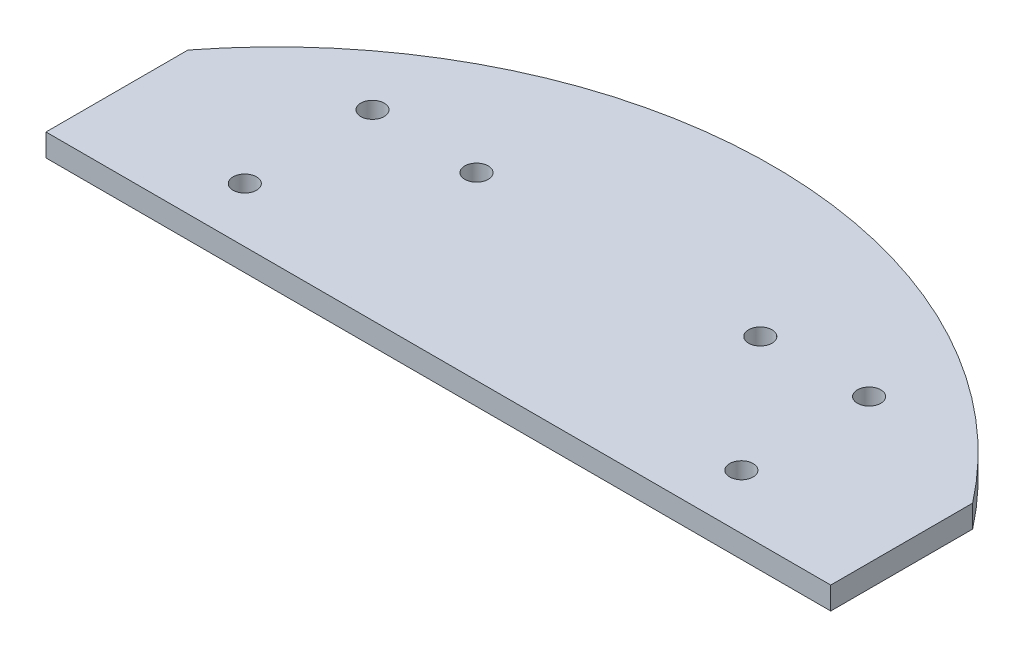
SolidWorks part; units mm, degrees
ref_plane "Front Plane" through (0, 0, 0) normal (0, 0, 1) x (1, 0, 0)
ref_plane "Top Plane" through (0, 0, 0) normal (0, 1, 0) x (1, 0, 0)
ref_plane "Right Plane" through (0, 0, 0) normal (1, 0, 0) x (0, 0, -1)
sketch "Sketch1" plane through (0, 0, 0) normal (0, 1, 0) x (1, 0, 0)
  line L0 (0, 70) -> (0, 22.9088) construction
  line L1 (35, 22.9088) -> (35, 60.6218) construction
  line L3 (0, 0) -> (49.4975, 49.4975) construction
  line L4 (0, 0) -> (26.7878, 64.6716) construction
  line L15 (0, 0) -> (-26.7878, 64.6716) construction
  line L16 (0, 0) -> (-49.4975, 49.4975) construction
  line L18 (-55.3067, 42.9088) -> (-55.3067, 22.9088)
  line L19 (55.3067, 42.9088) -> (55.3067, 22.9088)
  line L20 (-55.3067, 22.9088) -> (55.3067, 22.9088)
  arc A14 (55.3067, 42.9088) -> (-55.3067, 42.9088) centre (0, 0) ccw
  circle A17 centre (35, 48.6218) radius 1.65
  circle A18 centre (35, 30.6218) radius 1.65
  circle A19 centre (-35, 30.6218) radius 1.65
  circle A20 centre (-35, 48.6218) radius 1.65
  circle A21 centre (20, 48.2843) radius 1.65
  circle A22 centre (-20, 48.2843) radius 1.65
  point P21 (0, 0)
  point P22 (0, 0)
  point P23 (0, 0)
  dimension "D1" = 3.3
  dimension "D5" = 12
  dimension "D9" = 20
  dimension "D6" = 3.3
  dimension "D2" = 35
  dimension "D3" = 18
  dimension "D4" = 22.5
  dimension "D7" = 20
  dimension "D8" = 45
  dimension "D10" = 22.5
  dimension "D11" = 45
extrude "Boss-Extrude2" add sketch "Sketch1" along normal blind 3.175
